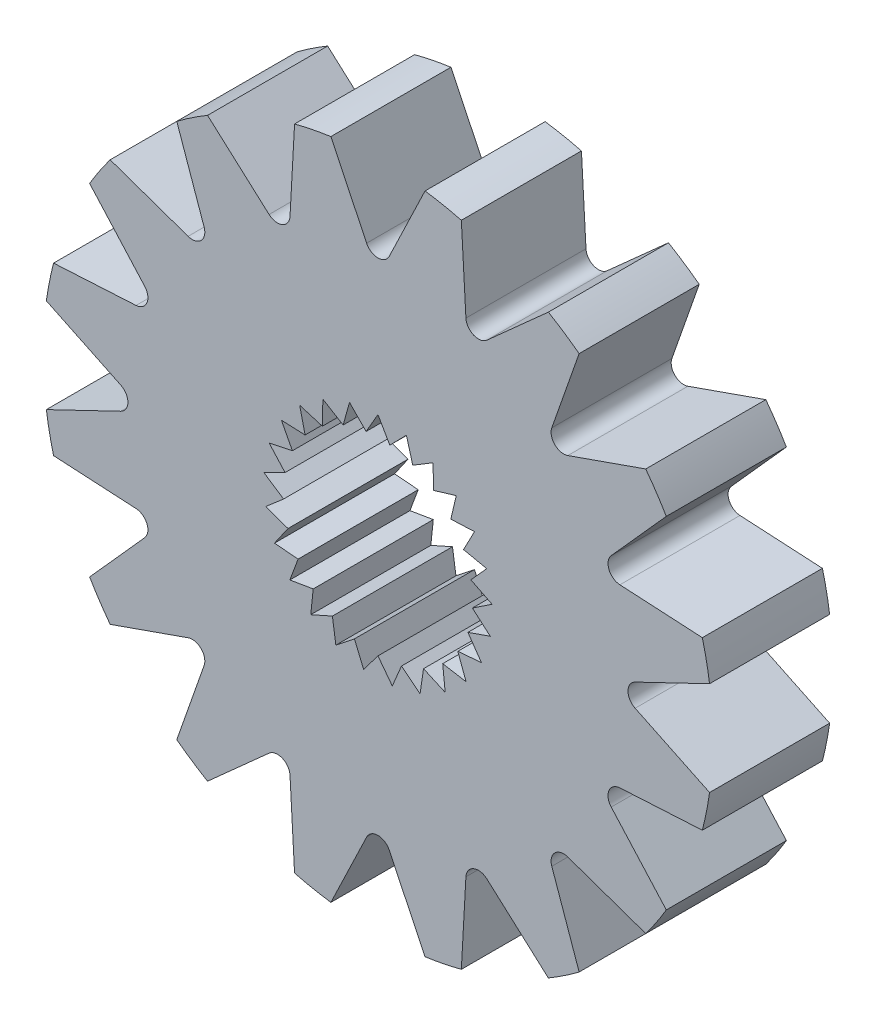
SolidWorks part; units mm, degrees
ref_plane "Front Plane" through (0, 0, 0) normal (0, 0, 1) x (1, 0, 0)
ref_plane "Top Plane" through (0, 0, 0) normal (0, 1, 0) x (1, 0, 0)
ref_plane "Right Plane" through (0, 0, 0) normal (1, 0, 0) x (0, 0, -1)
sketch "Sketch1" plane through (0, 0, 0) normal (0, 0, 1) x (1, 0, 0)
  line L0 (0, 3.048) -> (0, 0) construction
  line L1 (0, 3.048) -> (-0.3159, 2.5008)
  line L2 (0, 3.048) -> (0.3159, 2.5008)
  line L3 (-0.3159, 2.5008) -> (0.3159, 2.5008) construction
  line L4 (0.758, 2.9522) -> (0.3159, 2.5008)
  line L5 (0.758, 2.9522) -> (0.9279, 2.3437)
  line L6 (0.3159, 2.5008) -> (0.9279, 2.3437) construction
  line L7 (1.4684, 2.671) -> (0.9279, 2.3437)
  line L8 (1.4684, 2.671) -> (1.4816, 2.0393)
  line L9 (0.9279, 2.3437) -> (1.4816, 2.0393) construction
  line L10 (2.0865, 2.2219) -> (1.4816, 2.0393)
  line L11 (2.0865, 2.2219) -> (1.9422, 1.6067)
  line L12 (1.4816, 2.0393) -> (1.9422, 1.6067) construction
  line L13 (2.5735, 1.6332) -> (1.9422, 1.6067)
  line L14 (2.5735, 1.6332) -> (2.2808, 1.0733)
  line L15 (1.9422, 1.6067) -> (2.2808, 1.0733) construction
  line L16 (2.8988, 0.9419) -> (2.2808, 1.0733)
  line L17 (2.8988, 0.9419) -> (2.476, 0.4723)
  line L18 (2.2808, 1.0733) -> (2.476, 0.4723) construction
  line L19 (3.042, 0.1914) -> (2.476, 0.4723)
  line L20 (3.042, 0.1914) -> (2.5157, -0.1583)
  line L21 (2.476, 0.4723) -> (2.5157, -0.1583) construction
  line L22 (2.994, -0.5711) -> (2.5157, -0.1583)
  line L23 (2.994, -0.5711) -> (2.3973, -0.7789)
  line L24 (2.5157, -0.1583) -> (2.3973, -0.7789) construction
  line L25 (2.7579, -1.2978) -> (2.3973, -0.7789)
  line L26 (2.7579, -1.2978) -> (2.1283, -1.3506)
  line L27 (2.3973, -0.7789) -> (2.1283, -1.3506) construction
  line L28 (2.3485, -1.9429) -> (2.1283, -1.3506)
  line L29 (2.3485, -1.9429) -> (1.7255, -1.8375)
  line L30 (2.1283, -1.3506) -> (1.7255, -1.8375) construction
  line L31 (1.7916, -2.4659) -> (1.7255, -1.8375)
  line L32 (1.7916, -2.4659) -> (1.2143, -2.2089)
  line L33 (1.7255, -1.8375) -> (1.2143, -2.2089) construction
  line L34 (1.122, -2.834) -> (1.2143, -2.2089)
  line L35 (1.122, -2.834) -> (0.6269, -2.4415)
  line L36 (1.2143, -2.2089) -> (0.6269, -2.4415) construction
  line L37 (0.382, -3.024) -> (0.6269, -2.4415)
  line L38 (0.382, -3.024) -> (0, -2.5207)
  line L39 (0.6269, -2.4415) -> (0, -2.5207) construction
  line L40 (-0.382, -3.024) -> (0, -2.5207)
  line L41 (-0.382, -3.024) -> (-0.6269, -2.4415)
  line L42 (0, -2.5207) -> (-0.6269, -2.4415) construction
  line L43 (-1.122, -2.834) -> (-0.6269, -2.4415)
  line L44 (-1.122, -2.834) -> (-1.2143, -2.2089)
  line L45 (-0.6269, -2.4415) -> (-1.2143, -2.2089) construction
  line L46 (-1.7916, -2.4659) -> (-1.2143, -2.2089)
  line L47 (-1.7916, -2.4659) -> (-1.7255, -1.8375)
  line L48 (-1.2143, -2.2089) -> (-1.7255, -1.8375) construction
  line L49 (-2.3485, -1.9429) -> (-1.7255, -1.8375)
  line L50 (-2.3485, -1.9429) -> (-2.1283, -1.3506)
  line L51 (-1.7255, -1.8375) -> (-2.1283, -1.3506) construction
  line L52 (-2.7579, -1.2978) -> (-2.1283, -1.3506)
  line L53 (-2.7579, -1.2978) -> (-2.3973, -0.7789)
  line L54 (-2.1283, -1.3506) -> (-2.3973, -0.7789) construction
  line L55 (-2.994, -0.5711) -> (-2.3973, -0.7789)
  line L56 (-2.994, -0.5711) -> (-2.5157, -0.1583)
  line L57 (-2.3973, -0.7789) -> (-2.5157, -0.1583) construction
  line L58 (-3.042, 0.1914) -> (-2.5157, -0.1583)
  line L59 (-3.042, 0.1914) -> (-2.476, 0.4723)
  line L60 (-2.5157, -0.1583) -> (-2.476, 0.4723) construction
  line L61 (-2.8988, 0.9419) -> (-2.476, 0.4723)
  line L62 (-2.8988, 0.9419) -> (-2.2808, 1.0733)
  line L63 (-2.476, 0.4723) -> (-2.2808, 1.0733) construction
  line L64 (-2.5735, 1.6332) -> (-2.2808, 1.0733)
  line L65 (-2.5735, 1.6332) -> (-1.9422, 1.6067)
  line L66 (-2.2808, 1.0733) -> (-1.9422, 1.6067) construction
  line L67 (-2.0865, 2.2219) -> (-1.9422, 1.6067)
  line L68 (-2.0865, 2.2219) -> (-1.4816, 2.0393)
  line L69 (-1.9422, 1.6067) -> (-1.4816, 2.0393) construction
  line L70 (-1.4684, 2.671) -> (-1.4816, 2.0393)
  line L71 (-1.4684, 2.671) -> (-0.9279, 2.3437)
  line L72 (-1.4816, 2.0393) -> (-0.9279, 2.3437) construction
  line L73 (-0.758, 2.9522) -> (-0.9279, 2.3437)
  line L74 (-0.758, 2.9522) -> (-0.3159, 2.5008)
  line L75 (-0.9279, 2.3437) -> (-0.3159, 2.5008) construction
  circle A1 centre (0, 0) radius 8.9262
  point P0 (0, 2.5008)
  point P12 (0.6219, 2.4222)
  point P16 (1.2048, 2.1915)
  point P20 (1.7119, 1.823)
  point P24 (2.1115, 1.34)
  point P28 (2.3784, 0.7728)
  point P32 (2.4959, 0.157)
  point P36 (2.4565, -0.4686)
  point P40 (2.2628, -1.0648)
  point P44 (1.9269, -1.5941)
  point P48 (1.4699, -2.0232)
  point P52 (0.9206, -2.3252)
  point P56 (0.3134, -2.4811)
  point P60 (-0.3134, -2.4811)
  point P64 (-0.9206, -2.3252)
  point P68 (-1.4699, -2.0232)
  point P72 (-1.9269, -1.5941)
  point P76 (-2.2628, -1.0648)
  point P80 (-2.4565, -0.4686)
  point P84 (-2.4959, 0.157)
  point P88 (-2.3784, 0.7728)
  point P92 (-2.1115, 1.34)
  point P96 (-1.7119, 1.823)
  point P100 (-1.2048, 2.1915)
  point P104 (-0.6219, 2.4222)
  dimension "D1" = 25
  dimension "D3" = 17.8524
  dimension "D2" = 60
extrude "Boss-Extrude1" add sketch "Sketch1" along normal blind 3.2004
sketch "Sketch2" plane through (0, 0, 3.2004) normal (0, 0, 1) x (1, 0, 0)
  line L0 (-1.2551, 8.8375) -> (1.2551, 8.8375) construction
  line L1 (-1.2551, 8.8375) -> (-0.3019, 6.8539)
  line L2 (0, 0) -> (0.8769, 8.8375) construction
  line L3 (0.3019, 6.8539) -> (1.2551, 8.8375)
  line L4 (-0.3019, 6.8539) -> (0.3019, 6.8539) construction
  line L5 (2.9018, 6.2167) -> (4.5416, 7.6845)
  line L6 (-0.7785, 7.8457) -> (0.7785, 7.8457) construction
  line L7 (2.2224, 8.6451) -> (2.344, 6.4477)
  line L8 (5.0599, 4.633) -> (7.1366, 5.3616)
  line L9 (5.3616, 7.1366) -> (4.633, 5.0599)
  line L10 (6.4477, 2.344) -> (8.6451, 2.2224)
  line L11 (7.6845, 4.5416) -> (6.2167, 2.9018)
  line L12 (6.8539, -0.3019) -> (8.8375, -1.2551)
  line L13 (8.8375, 1.2551) -> (6.8539, 0.3019)
  line L14 (6.2167, -2.9018) -> (7.6845, -4.5416)
  line L15 (8.6451, -2.2224) -> (6.4477, -2.344)
  line L16 (4.633, -5.0599) -> (5.3616, -7.1366)
  line L17 (7.1366, -5.3616) -> (5.0599, -4.633)
  line L18 (2.344, -6.4477) -> (2.2224, -8.6451)
  line L19 (4.5416, -7.6845) -> (2.9018, -6.2167)
  line L20 (-0.3019, -6.8539) -> (-1.2551, -8.8375)
  line L21 (1.2551, -8.8375) -> (0.3019, -6.8539)
  line L22 (-2.9018, -6.2167) -> (-4.5416, -7.6845)
  line L23 (-2.2224, -8.6451) -> (-2.344, -6.4477)
  line L24 (-5.0599, -4.633) -> (-7.1366, -5.3616)
  line L25 (-5.3616, -7.1366) -> (-4.633, -5.0599)
  line L26 (-6.4477, -2.344) -> (-8.6451, -2.2224)
  line L27 (-7.6845, -4.5416) -> (-6.2167, -2.9018)
  line L28 (-6.8539, 0.3019) -> (-8.8375, 1.2551)
  line L29 (-8.8375, -1.2551) -> (-6.8539, -0.3019)
  line L30 (-6.2167, 2.9018) -> (-7.6845, 4.5416)
  line L31 (-8.6451, 2.2224) -> (-6.4477, 2.344)
  line L32 (-4.633, 5.0599) -> (-5.3616, 7.1366)
  line L33 (-7.1366, 5.3616) -> (-5.0599, 4.633)
  line L34 (-2.344, 6.4477) -> (-2.2224, 8.6451)
  line L35 (-4.5416, 7.6845) -> (-2.9018, 6.2167)
  line L180 (0, 8.8375) -> (0, 0) construction
  arc A0 (0.3019, 6.8539) -> (-0.3019, 6.8539) centre (0, 6.999) cw
  arc A1 (1.2551, 8.8375) -> (-1.2551, 8.8375) centre (0, 0) ccw
  arc A2 (2.9018, 6.2167) -> (2.344, 6.4477) centre (2.6784, 6.4662) cw
  circle A3 centre (0, 0) radius 8.9262 construction
  arc A4 (4.5416, 7.6845) -> (2.2224, 8.6451) centre (0, 0) ccw
  arc A5 (5.0599, 4.633) -> (4.633, 5.0599) centre (4.949, 4.949) cw
  arc A6 (7.1366, 5.3616) -> (5.3616, 7.1366) centre (0, 0) ccw
  arc A7 (6.4477, 2.344) -> (6.2167, 2.9018) centre (6.4662, 2.6784) cw
  arc A8 (8.6451, 2.2224) -> (7.6845, 4.5416) centre (0, 0) ccw
  arc A9 (6.8539, -0.3019) -> (6.8539, 0.3019) centre (6.999, 0) cw
  arc A10 (8.8375, -1.2551) -> (8.8375, 1.2551) centre (0, 0) ccw
  arc A11 (6.2167, -2.9018) -> (6.4477, -2.344) centre (6.4662, -2.6784) cw
  arc A12 (7.6845, -4.5416) -> (8.6451, -2.2224) centre (0, 0) ccw
  arc A13 (4.633, -5.0599) -> (5.0599, -4.633) centre (4.949, -4.949) cw
  arc A14 (5.3616, -7.1366) -> (7.1366, -5.3616) centre (0, 0) ccw
  arc A15 (2.344, -6.4477) -> (2.9018, -6.2167) centre (2.6784, -6.4662) cw
  arc A16 (2.2224, -8.6451) -> (4.5416, -7.6845) centre (0, 0) ccw
  arc A17 (-0.3019, -6.8539) -> (0.3019, -6.8539) centre (0, -6.999) cw
  arc A18 (-1.2551, -8.8375) -> (1.2551, -8.8375) centre (0, 0) ccw
  arc A19 (-2.9018, -6.2167) -> (-2.344, -6.4477) centre (-2.6784, -6.4662) cw
  arc A20 (-4.5416, -7.6845) -> (-2.2224, -8.6451) centre (0, 0) ccw
  arc A21 (-5.0599, -4.633) -> (-4.633, -5.0599) centre (-4.949, -4.949) cw
  arc A22 (-7.1366, -5.3616) -> (-5.3616, -7.1366) centre (0, 0) ccw
  arc A23 (-6.4477, -2.344) -> (-6.2167, -2.9018) centre (-6.4662, -2.6784) cw
  arc A24 (-8.6451, -2.2224) -> (-7.6845, -4.5416) centre (0, 0) ccw
  arc A25 (-6.8539, 0.3019) -> (-6.8539, -0.3019) centre (-6.999, 0) cw
  arc A26 (-8.8375, 1.2551) -> (-8.8375, -1.2551) centre (0, 0) ccw
  arc A27 (-6.2167, 2.9018) -> (-6.4477, 2.344) centre (-6.4662, 2.6784) cw
  arc A28 (-7.6845, 4.5416) -> (-8.6451, 2.2224) centre (0, 0) ccw
  arc A29 (-4.633, 5.0599) -> (-5.0599, 4.633) centre (-4.949, 4.949) cw
  arc A30 (-5.3616, 7.1366) -> (-7.1366, 5.3616) centre (0, 0) ccw
  arc A31 (-2.344, 6.4477) -> (-2.9018, 6.2167) centre (-2.6784, 6.4662) cw
  arc A32 (-2.2224, 8.6451) -> (-4.5416, 7.6845) centre (0, 0) ccw
  point P1 (0, 7.8457)
  point P92 (0, 0)
  point P132 (0, 0)
  point P212 (0, 0)
  dimension "D1" = 0.9918
  dimension "D2" = 20
  dimension "D3" = 16
  dimension "D5" = 1.557
extrude "Cut-Extrude1" cut sketch "Sketch2" against normal up to surface (3.2004 mm away) up to face at (8.9262, 0, 0)
sketch "Sketch3" plane through (0, 0, 3.2004) normal (0, 0, 1) x (1, 0, 0)
  circle A0 centre (0, 0) radius 7.9344 construction
  circle A1 centre (0, 0) radius 8.9262 construction
  dimension "D1" = 15.8688
